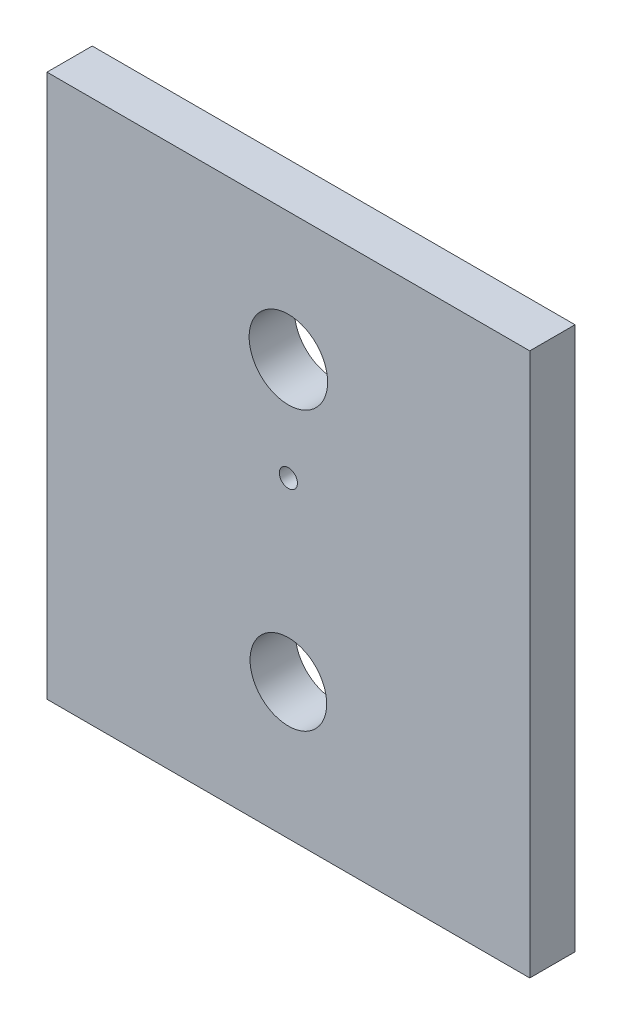
SolidWorks part; units mm, degrees
ref_plane "Front Plane" through (0, 0, 0) normal (0, 0, 1) x (1, 0, 0)
ref_plane "Top Plane" through (0, 0, 0) normal (0, 1, 0) x (1, 0, 0)
ref_plane "Right Plane" through (0, 0, 0) normal (1, 0, 0) x (0, 0, -1)
sketch "Sketch2" plane through (0, 0, 0) normal (0, 0, 1) x (1, 0, 0)
  line L1 (-80, -95) -> (80, -95)
  line L2 (-80, -95) -> (-80, 85)
  line L3 (-80, 85) -> (80, 85)
  line L4 (80, -95) -> (80, 85)
  point P0 (0, 0)
  dimension "D1" = 160
  dimension "D2" = 180
extrude "Boss-Extrude1" add sketch "Sketch2" along normal blind 15
sketch "Sketch3" plane through (0, 0, 15) normal (0, 0, 1) x (1, 0, 0)
  line L0 (0, 85) -> (0, 0) construction
  line L1 (80, 85) -> (-80, 85) construction
  point P5 (0, 42.5)
hole_wizard "Ø20.0 (20) Diameter Hole1" positions "Sketch5" profile "Sketch6" hole size "Ø20.0" standard "ANSI Metric" end condition through all
sketch "Sketch5" plane through (0, 0, 15) normal (0, 0, 1) x (1, 0, 0)
  point P0 (0, 42.5)
sketch "Sketch6" plane through (0, 42.5, 15) normal (1, 0, 0) x (0, -1, 0)
  line L0 (0, 0) -> (0, 15)
  line L1 (0, 15) -> (13.005, 15)
  line L2 (13.005, 15) -> (13.005, 0)
  line L5 (13.005, 0) -> (0, 0)
  line L11 (0, -6.35) -> (0, 107.95) construction
  dimension "Thru Hole Dia." = 26.01
  dimension "Thru Hole Depth" = 15
sketch "Sketch7" plane through (0, 0, 15) normal (0, 0, 1) x (1, 0, 0)
  point P0 (0, 8.5)
  dimension "D1" = 34
hole_wizard "Ø6.0mm Dowel Hole1" positions "Sketch9" profile "Sketch8" hole size "Ø6.0" standard "ANSI Metric"
sketch "Sketch9" plane through (0, 0, 15) normal (0, 0, 1) x (1, 0, 0)
  point P0 (0, 8.5)
sketch "Sketch8" plane through (0, 8.5, 15) normal (1, 0, 0) x (0, -1, 0)
  line L0 (0, 0) -> (0, 41.8026)
  line L1 (0, 41.8026) -> (3, 40)
  line L2 (3, 40) -> (3, 0)
  line L5 (3, 0) -> (0, 0)
  line L10 (0, 41.8026) -> (-3, 40) construction
  line L11 (0, -6.35) -> (0, 107.95) construction
  dimension "Hole Dia." = 6
  dimension "Hole Depth" = 40
  dimension "Drill Angle" = 118
sketch "Sketch10" plane through (0, 0, 15) normal (0, 0, 1) x (1, 0, 0)
  circle A0 centre (0, -50) radius 12.7
extrude "Cut-Extrude1" cut sketch "Sketch10" against normal through all contours A0
